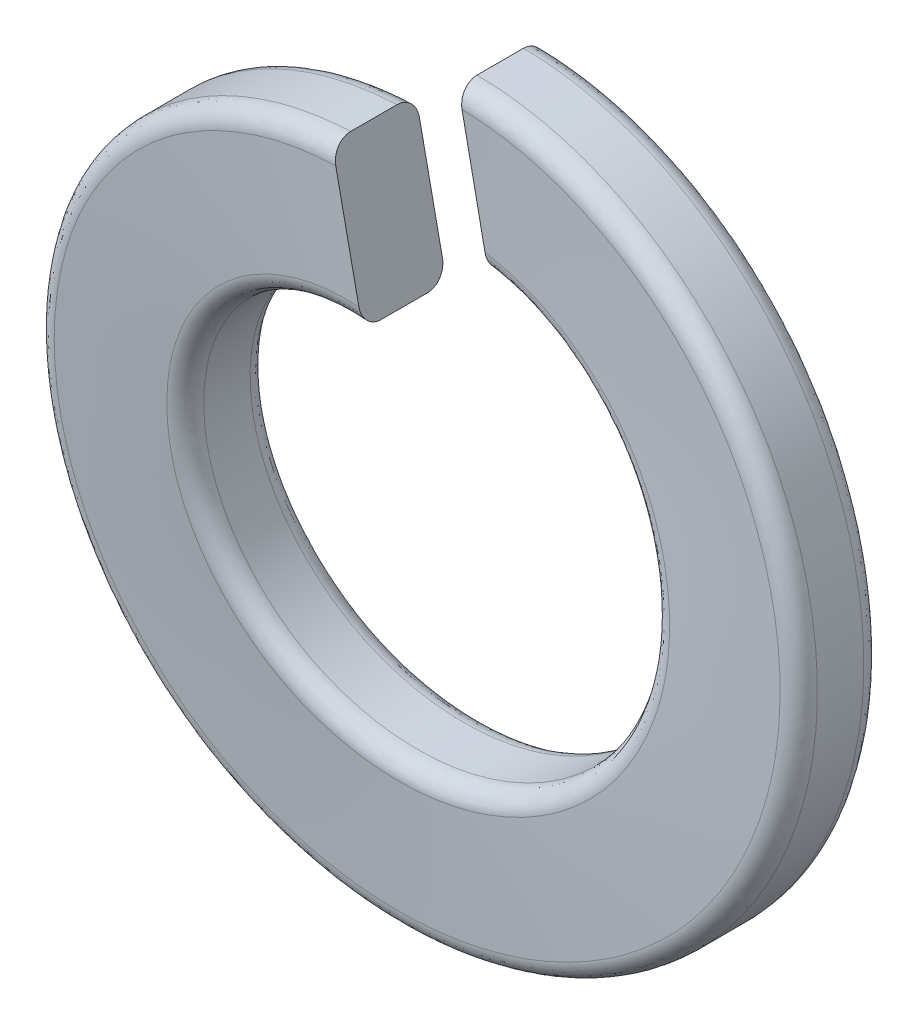
SolidWorks part; units mm, degrees
ref_plane "Front Plane" through (0, 0, 0) normal (0, 0, 1) x (1, 0, 0)
ref_plane "Top Plane" through (0, 0, 0) normal (0, 1, 0) x (1, 0, 0)
ref_plane "Right Plane" through (0, 0, 0) normal (1, 0, 0) x (0, 0, -1)
sketch "Sketch1" plane through (0, 0, 0) normal (0, 0, 1) x (1, 0, 0)
  line L0 (0, -3.8) -> (0, 3.8) construction
  line L1 (-0.1658, 3.7964) -> (0.1691, 2.1935) construction
  line L2 (0, 0) -> (-1.1, -1.9053) construction
  line L3 (0, 2.2) -> (-0.3312, 3.7855) construction
  line L4 (0, 0) -> (-0.3312, 3.7855) construction
  line L5 (-0.1658, 3.7964) -> (0, 0) construction
  circle A0 centre (0, 0) radius 3.8 construction
  circle A1 centre (0, 0) radius 2.2 construction
  point P6 (0, -2.2)
  dimension "ID" = 4.4
  dimension "OD" = 7.6
  dimension "D2" = 5
  dimension "D1" = 30
  dimension "D3" = 2.5
sketch "Sketch2" plane through (0, 0, 0) normal (1, 0, 0) x (0, 0, -1)
  line L0 (-1.05, 0) -> (1.05, 0) construction
  line L1 (0, -3.8) -> (0, 3.8) construction
  line L2 (-1.05, 3.8) -> (-0.15, 3.8) construction
  line L3 (-1.05, 3.8) -> (-1.05, 2.2) construction
  line L4 (-1.05, 2.2) -> (-0.15, 2.2) construction
  line L5 (-0.15, 3.8) -> (-0.15, 2.2) construction
  line L6 (0, -3.8) -> (0, 3.8) construction
  line L12 (-0.45, -2.2) -> (0.45, -2.2) construction
  line L13 (-0.45, -2.2) -> (-0.45, -3.8) construction
  line L14 (-0.45, -3.8) -> (0.45, -3.8) construction
  line L15 (0.45, -2.2) -> (0.45, -3.8) construction
  point P8 (-0.6, 3.8)
  point P13 (0.45, -3.6)
  point P15 (1.05, 3.8)
  point P19 (0.6, 3.8)
  dimension "Thickness" = 0.9
  dimension "Helix Height" = 1.2
  dimension "Height" = 2.1
  dimension "Radius" = 0.2
ref_plane "Plane1" through (0, 0, 0.6) normal (0, 0, 1) x (1, 0, 0)
sketch "Sketch3" plane through (0, 0, 0.6) normal (0, 0, 1) x (1, 0, 0)
  circle A0 centre (0, 0) radius 3.8 construction
  circle A1 centre (0, 0) radius 3.8
curve "Helix/Spiral1" pitch 1.2012 height 1.2 turns 0.999
ref_plane "Plane2" through (0.4403, 0.092, 0) normal (0.9789, 0.2045, 0) x (0.0072, -0.0342, -0.9994)
sketch "Sketch4" plane through (0.4699, -0.0497, 0.0051) normal (0.9789, 0.2045, 0) x (0.0072, -0.0342, -0.9994)
  line L0 (-1.1794, 3.8255) -> (-0.28, 3.857) construction
  line L10 (-1.1247, 2.2603) -> (-0.2252, 2.2918) construction
  line L12 (-1.1813, 3.8791) -> (-0.2819, 3.9105)
  line L13 (-0.2819, 3.9105) -> (-0.2252, 2.2918)
  line L14 (-1.1247, 2.2603) -> (-0.2252, 2.2918)
  line L15 (-1.1813, 3.8791) -> (-1.1247, 2.2603)
sweep "Sweep1" add profiles "Sketch4" path "Helix/Spiral1"
sketch "Sketch5" plane through (0, 0, 0) normal (0, 0, 1) x (1, 0, 0)
  line L0 (0, 2.2) -> (-0.3312, 3.7855) construction
  line L1 (-0.1658, 3.7964) -> (0.1691, 2.1935) construction
  line L2 (0, 2.2) -> (-0.3312, 3.7855)
  line L3 (-0.1658, 3.7964) -> (0.1691, 2.1935)
  circle A0 centre (0, 0) radius 2.2 construction
  circle A1 centre (0, 0) radius 3.8 construction
  arc A2 (0.1691, 2.1935) -> (0, 2.2) centre (0, 0) ccw
  arc A3 (-0.1658, 3.7964) -> (-0.3312, 3.7855) centre (0, 0) ccw
extrude "Cut-Extrude1" cut sketch "Sketch5" against normal through all
fillet "Fillet1" radius 0.2 4 edges
equation "\"D3@Helix/Spiral1\"=\"Helix Height@Sketch2\""
equation "\"D7@Helix/Spiral1\"=90+\"D2@Sketch1\""
equation "\"D1@Fillet1\"=\"Radius@Sketch2\""
equation "\"D3@Sketch1\"=\"D2@Sketch1\"/2"
